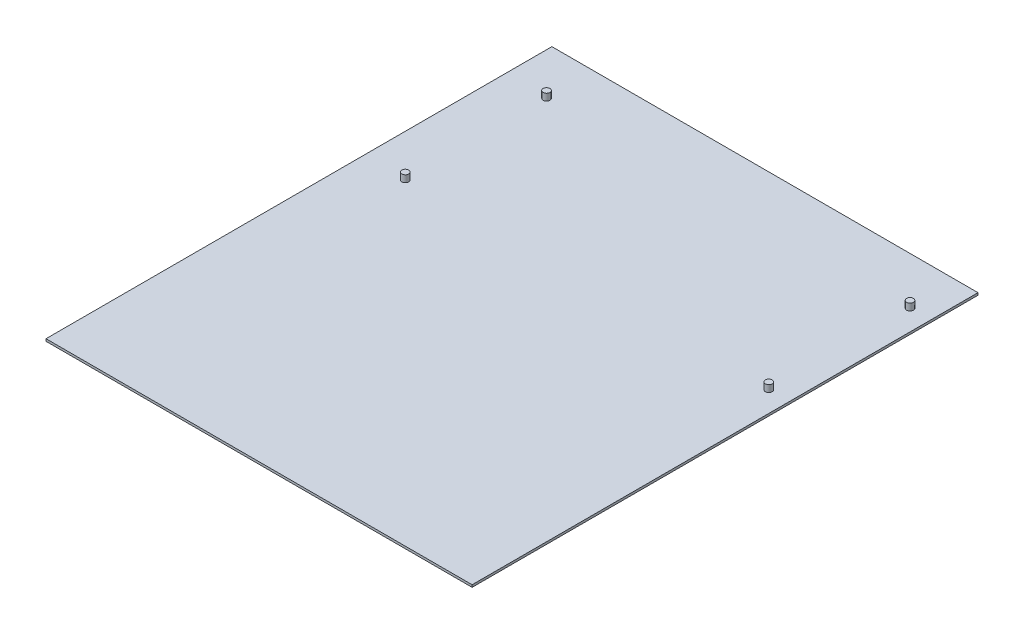
SolidWorks part; units mm, degrees
ref_plane "Front Plane" through (0, 0, 0) normal (0, 0, 1) x (1, 0, 0)
ref_plane "Top Plane" through (0, 0, 0) normal (0, 1, 0) x (1, 0, 0)
ref_plane "Right Plane" through (0, 0, 0) normal (1, 0, 0) x (0, 0, -1)
sketch "Sketch1" plane through (0, 0, 0) normal (0, 1, 0) x (1, 0, 0)
  line L1 (-56.1029, 186.4626) -> (130.8971, 186.4626)
  line L2 (-56.1029, 186.4626) -> (-56.1029, -35.5374)
  line L3 (-56.1029, -35.5374) -> (130.8971, -35.5374)
  line L4 (130.8971, 186.4626) -> (130.8971, -35.5374)
  dimension "D1" = 187
  dimension "D2" = 222
extrude "Boss-Extrude1" add sketch "Sketch1" along normal blind 1
sketch "Sketch2" plane through (0, 1, 0) normal (0, 1, 0) x (1, 0, 0)
  line L0 (130.8971, 186.4626) -> (-56.1029, 186.4626) construction
  line L2 (81.8971, 187.4626) -> (81.8971, 186.4626) construction
  line L4 (130.8971, -35.5374) -> (130.8971, 186.4626) construction
  circle A0 centre (121.8971, 165.6326) radius 1.5
  circle A1 centre (-37.6149, 165.6326) radius 1.5
  circle A2 centre (121.8971, 103.6566) radius 1.5
  circle A3 centre (-37.6149, 103.6526) radius 1.5
  dimension "D2" = 3
  dimension "D3" = 3
  dimension "D4" = 3
  dimension "D5" = 61.976
  dimension "D6" = 159.512
  dimension "D7" = 61.98
  dimension "D8" = 0
  dimension "D9" = 0
  dimension "D10" = 0
  dimension "D11" = 20.83
  dimension "D12" = 40
extrude "Boss-Extrude2" add sketch "Sketch2" along normal blind 3
